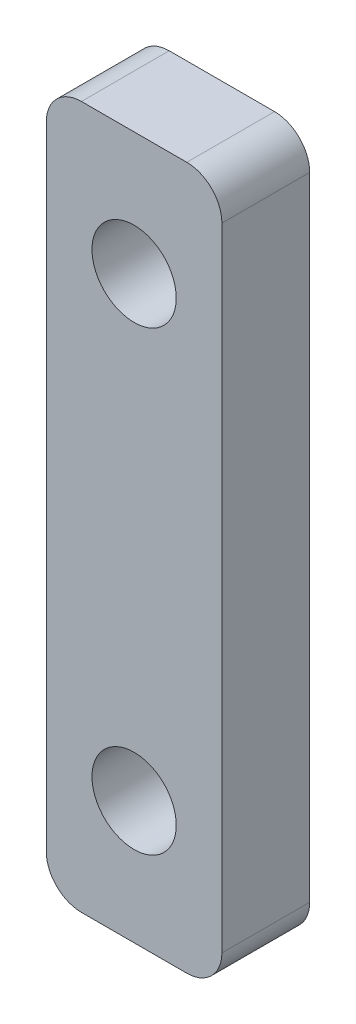
SolidWorks part; units mm, degrees
ref_plane "Front Plane" through (0, 0, 0) normal (0, 0, 1) x (1, 0, 0)
ref_plane "Top Plane" through (0, 0, 0) normal (0, 1, 0) x (1, 0, 0)
ref_plane "Right Plane" through (0, 0, 0) normal (1, 0, 0) x (0, 0, -1)
sketch "Sketch1" plane through (0, 0, 0) normal (0, 0, 1) x (1, 0, 0)
  line L1 (-5, 20) -> (5, 20)
  line L2 (-5, 20) -> (-5, -20)
  line L3 (-5, -20) -> (5, -20)
  line L4 (5, 20) -> (5, -20)
  line L5 (0, -20) -> (0, 20) construction
  line L6 (-5, 0) -> (5, 0) construction
  circle A0 centre (0, 13) radius 2.4
  circle A1 centre (0, -13) radius 2.4
  point P0 (0, 0)
  dimension "D3" = 4.8
  dimension "D1" = 40
  dimension "D2" = 10
  dimension "D4" = 13
extrude "Boss-Extrude1" add sketch "Sketch1" along normal blind 5
fillet "Fillet1" radius 2 4 edges at (5, 20, 2.5) (5, -20, 2.5) (-5, -20, 2.5) (-5, 20, 2.5)
